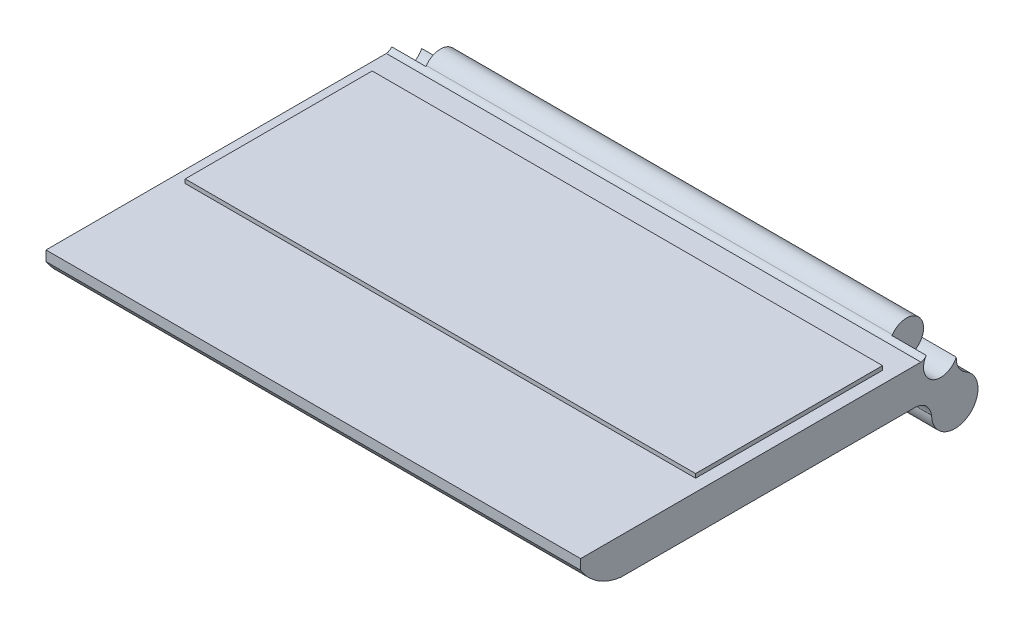
SolidWorks part; units mm, degrees
ref_plane "Front Plane" through (0, 0, 0) normal (0, 0, 1) x (1, 0, 0)
ref_plane "Top Plane" through (0, 0, 0) normal (0, 1, 0) x (1, 0, 0)
ref_plane "Right Plane" through (0, 0, 0) normal (1, 0, 0) x (0, 0, -1)
sketch "Sketch1" plane through (0, 0, 0) normal (0, 1, 0) x (1, 0, 0)
  line L1 (-132.5, -85) -> (132.5, -85)
  line L2 (-132.5, -85) -> (-132.5, 85)
  line L3 (-132.5, 85) -> (132.5, 85)
  line L4 (132.5, -85) -> (132.5, 85)
  line L5 (-132.5, -85) -> (132.5, 85) construction
  line L6 (-132.5, 85) -> (132.5, -85) construction
  point P0 (0, 0)
  dimension "D1" = 265
  dimension "D2" = 170
extrude "Boss-Extrude1" add sketch "Sketch1" along normal blind 18
sketch "Sketch2" plane through (132.5, 0, 0) normal (1, 0, 0) x (0, 0, -1)
  line L0 (-85, 0) -> (85, 0) construction
  line L1 (-85, 18) -> (-85, 0) construction
  line L2 (-85, 18) -> (85, 18) construction
  arc A0 (-85, 13) -> (-65, 0) centre (-61.6042, 27.1089) ccw
  dimension "D1" = 20
  dimension "D2" = 5
extrude "Cut-Extrude1" cut sketch "Sketch2" against normal through all and the other way through all flip side to cut
sketch "Sketch3" plane through (-132.5, 0, 0) normal (-1, 0, 0) x (0, 0, 1)
  line L0 (-85, 18) -> (-85, 0) construction
  line L1 (-85, 18) -> (85, 18) construction
  circle A0 centre (-93.5, 15) radius 8.5
  spline S0 degree 2 poles (-86.5393, 19.8783) (-85.2086, 17.7202) (-82.513, 18) knots 0 0 0 1 1 1
  spline S1 degree 2 poles (-95.241, 6.6802) (-89.3277, 4.6181) (-85, 0) knots 0 0 0 1 1 1
  line M4 (85, 18) -> (-85, 18)
  line M5 (-85, 18) -> (-85, 0)
  dimension "D1" = 17
  dimension "D2" = 3
extrude "Boss-Extrude2" add sketch "Sketch3" against normal blind 265 contours A0 S1 M5 | S0 A0 | S0 A0 M5 M4
sketch "Sketch4" plane through (0, 18, 0) normal (0, 1, 0) x (1, 0, 0)
  line L0 (-132.5, 83.6784) -> (-132.5, -85) construction
  line L1 (126.5, -22) -> (-126.5, -22)
  line L2 (126.5, -22) -> (126.5, 70.6784)
  line L3 (126.5, 70.6784) -> (-126.5, 70.6784)
  line L4 (-126.5, -22) -> (-126.5, 70.6784)
  line L5 (126.5, -22) -> (-126.5, 70.6784) construction
  line L6 (126.5, 70.6784) -> (-126.5, -22) construction
  line L7 (132.5, 83.6784) -> (-132.5, 83.6784) construction
  line L9 (-132.5, -85) -> (132.5, -85) construction
  point P0 (0, 24.3392)
  dimension "D1" = 6
  dimension "D2" = 13
  dimension "D3" = 63
extrude "Boss-Extrude3" add sketch "Sketch4" along normal blind 2
sketch "Sketch6" plane through (-132.5, 0, 0) normal (-1, 0, 0) x (0, 0, 1)
  line L0 (-1108.0991, -19) -> (48891.9009, -19) construction
  line L1 (-85, 0) -> (65, 0) construction
  line L2 (-112, -1009.9019) -> (-112, 48990.0981) construction
  line L3 (-102, -985) -> (-102, 49015) construction
  line L4 (-101.2038, 11.4081) -> (-78.6792, 0)
  arc A0 (-106.0053, 2.5966) -> (-89, -7.5) centre (-100.5, -7.5) ccw
  arc A2 (-86.5393, 19.8783) -> (-95.241, 6.6802) centre (-93.5, 15) ccw construction
  spline S0 degree 2 poles (-89, -7.5) (-87.2365, 0.6151) (-78.6792, 0) knots 0 0 0 1 1 1
  spline S1 degree 2 poles (-106.0053, 2.5966) (-101.0371, 5.738) (-101.2038, 11.4081) knots 0 0 0 1 1 1
  spline M1 degree 2 poles (-95.241, 6.6802) (-89.3277, 4.6181) (-85, 0) knots 0 0 0 1 1 1
  line M2 (-85, 0) -> (65, 0)
  arc M7 (-86.5393, 19.8783) -> (-95.241, 6.6802) centre (-93.5, 15) ccw
  dimension "D1" = 23
  dimension "D2" = 19
  dimension "D3" = 10
extrude "Boss-Extrude4" add sketch "Sketch6" against normal blind 265 contours A0 | S1 A0 S0 M2 M1 M7
sketch "Sketch8" plane through (-132.5, 0, 0) normal (-1, 0, 0) x (0, 0, 1)
  circle A0 centre (-93.5, 15) radius 8.5
  arc A1 (-86.5393, 19.8783) -> (-101.2038, 11.4081) centre (-93.5, 15) ccw construction
extrude "Cut-Extrude3" cut sketch "Sketch8" against normal blind 17
mirror "Mirror1" about plane through (0, 0, 0) normal (1, 0, 0) of "Cut-Extrude3"
